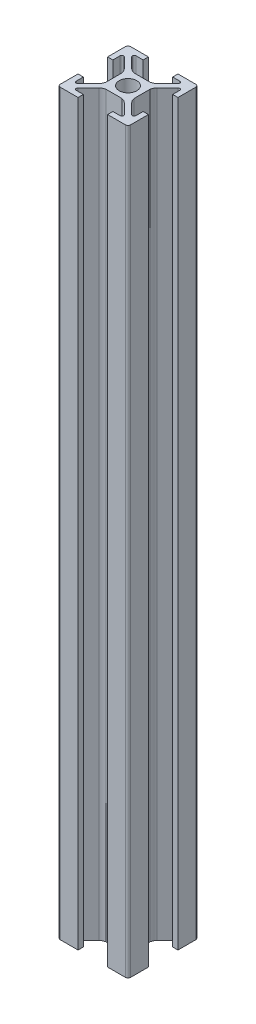
SolidWorks part; units mm, degrees
ref_plane "Front Plane" through (0, 0, 0) normal (0, 0, 1) x (1, 0, 0)
ref_plane "Top Plane" through (0, 0, 0) normal (0, 1, 0) x (1, 0, 0)
ref_plane "Right Plane" through (0, 0, 0) normal (1, 0, 0) x (0, 0, -1)
sketch "Sketch1" plane through (0, 0, 0) normal (0, 1, 0) x (1, 0, 0)
  line L0 (-3.611, 4.6716) -> (-6.5858, 7.6464)
  line L1 (9.25, -10) -> (4.2, -10)
  line L2 (10, -9.25) -> (10, -4.2)
  line L3 (9.25, 10) -> (4.2, 10)
  line L4 (-10, -9.25) -> (-10, -4.2)
  line L5 (10, -10) -> (-10, 10) construction
  line L6 (10, 10) -> (-10, -10) construction
  line L7 (2.2681, -4) -> (-2.2681, -4)
  line L8 (4, -2.2681) -> (4, 2.2681)
  line L9 (2.2681, 4) -> (-2.2681, 4)
  line L10 (-4, -2.2681) -> (-4, 2.2681)
  line L11 (4, -4) -> (-4, 4) construction
  line L12 (4, 4) -> (-4, -4) construction
  line L13 (-6.2322, 8.5) -> (-4.2, 8.5)
  line L14 (-4.2, 8.5) -> (-4.2, 10)
  line L15 (4.6716, 3.611) -> (7.6464, 6.5858)
  line L16 (8.5, 6.2322) -> (8.5, 4.2)
  line L17 (8.5, 4.2) -> (10, 4.2)
  line L18 (4.2, 8.5) -> (4.2, 10)
  line L19 (-8.5, 4.2) -> (-10, 4.2)
  line L20 (-8.5, 6.2322) -> (-8.5, 4.2)
  line L21 (-4.6716, 3.611) -> (-7.6464, 6.5858)
  line L22 (0, 10) -> (0, -10) construction
  line L23 (6.2322, 8.5) -> (4.2, 8.5)
  line L24 (3.611, 4.6716) -> (6.5858, 7.6464)
  line L25 (-55, 0) -> (55, 0) construction
  line L26 (3.611, -4.6716) -> (6.5858, -7.6464)
  line L27 (6.2322, -8.5) -> (4.2, -8.5)
  line L28 (-4.6716, -3.611) -> (-7.6464, -6.5858)
  line L29 (-8.5, -6.2322) -> (-8.5, -4.2)
  line L30 (-8.5, -4.2) -> (-10, -4.2)
  line L31 (4.2, -8.5) -> (4.2, -10)
  line L32 (8.5, -4.2) -> (10, -4.2)
  line L33 (8.5, -6.2322) -> (8.5, -4.2)
  line L34 (4.6716, -3.611) -> (7.6464, -6.5858)
  line L35 (-4.2, -8.5) -> (-4.2, -10)
  line L36 (-6.2322, -8.5) -> (-4.2, -8.5)
  line L37 (2.2681, -4) -> (-2.2681, -4)
  line L38 (10, -10) -> (4.2, -10)
  line L39 (-3.611, -4.6716) -> (-6.5858, -7.6464)
  line L40 (-4.2, 10) -> (-9.25, 10)
  line L41 (-10, 4.2) -> (-10, 9.25)
  line L42 (-4.2, -10) -> (-9.25, -10)
  line L43 (-4.2, -10) -> (-10, -10)
  line L44 (10, 4.2) -> (10, 9.25)
  circle A0 centre (0, 0) radius 2.5
  arc A1 (-8.5, 6.2322) -> (-7.6464, 6.5858) centre (-8, 6.2322) cw
  arc A2 (-6.5858, 7.6464) -> (-6.2322, 8.5) centre (-6.2322, 8) cw
  arc A3 (-3.611, 4.6716) -> (-2.2681, 4) centre (-1.7294, 6.7555) ccw
  arc A4 (-4.6716, 3.611) -> (-4, 2.2681) centre (-6.7555, 1.7294) cw
  arc A5 (4.6716, 3.611) -> (4, 2.2681) centre (6.7555, 1.7294) ccw
  arc A6 (3.611, 4.6716) -> (2.2681, 4) centre (1.7294, 6.7555) cw
  arc A7 (6.5858, 7.6464) -> (6.2322, 8.5) centre (6.2322, 8) ccw
  arc A8 (8.5, 6.2322) -> (7.6464, 6.5858) centre (8, 6.2322) ccw
  arc A9 (8.5, -6.2322) -> (7.6464, -6.5858) centre (8, -6.2322) cw
  arc A10 (6.5858, -7.6464) -> (6.2322, -8.5) centre (6.2322, -8) cw
  arc A11 (3.611, -4.6716) -> (2.2681, -4) centre (1.7294, -6.7555) ccw
  arc A12 (4.6716, -3.611) -> (4, -2.2681) centre (6.7555, -1.7294) cw
  arc A13 (-4.6716, -3.611) -> (-4, -2.2681) centre (-6.7555, -1.7294) ccw
  arc A14 (-3.611, -4.6716) -> (-2.2681, -4) centre (-1.7294, -6.7555) cw
  arc A15 (-6.5858, -7.6464) -> (-6.2322, -8.5) centre (-6.2322, -8) ccw
  arc A16 (-8.5, -6.2322) -> (-7.6464, -6.5858) centre (-8, -6.2322) ccw
  arc A17 (-9.25, -10) -> (-10, -9.25) centre (-9.25, -9.25) cw
  arc A18 (9.25, -10) -> (10, -9.25) centre (9.25, -9.25) ccw
  arc A19 (10, 9.25) -> (9.25, 10) centre (9.25, 9.25) ccw
  arc A20 (-9.25, 10) -> (-10, 9.25) centre (-9.25, 9.25) ccw
  point P0 (0, 0)
  point P18 (-8.5, 7.4393)
  point P24 (-7.4393, 8.5)
  point P50 (7.4393, 8.5)
  point P51 (8.5, 7.4393)
  point P86 (8.5, -7.4393)
  point P87 (7.4393, -8.5)
  point P88 (-7.4393, -8.5)
  point P89 (-8.5, -7.4393)
  dimension "D2" = 5
  dimension "D7" = 0.5
  dimension "D8" = 0.75
  dimension "D1" = 20
  dimension "D3" = 8
  dimension "D4" = 1.5
  dimension "D5" = 1.5
  dimension "D6" = 8.4
extrude "Boss-Extrude1" add sketch "Sketch1" along normal blind 210 contours L40 A20 L41 L19 L20 A1 L21 A4 L10 A13 L28 A16 L29 L30 L4 A17 L42 L35 L36 A15 L39 A14 L7 A11 L26 A10 L27 L31 L1 A18 L2 L32 L33 A9 L34 A12 L8 A5 L15 A8 L16 L17 L44 A19 L3 L18 L23 A7 L24 A6 L9
